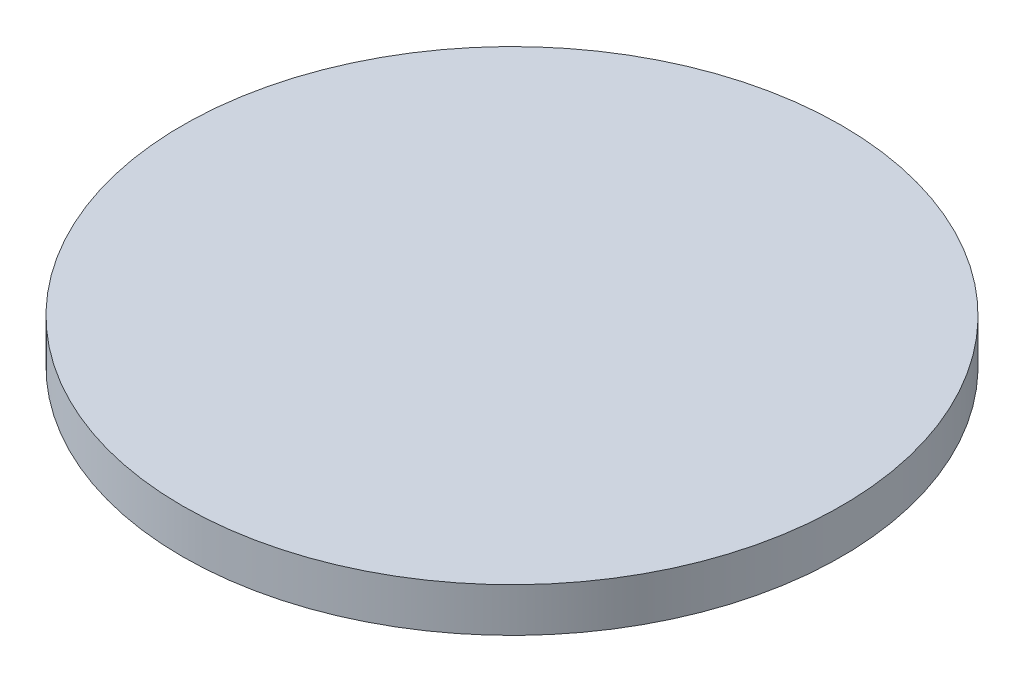
SolidWorks part; units mm, degrees
ref_plane "Front Plane" through (0, 0, 0) normal (0, 0, 1) x (1, 0, 0)
ref_plane "Top Plane" through (0, 0, 0) normal (0, 1, 0) x (1, 0, 0)
ref_plane "Right Plane" through (0, 0, 0) normal (1, 0, 0) x (0, 0, -1)
sketch "Sketch1" plane through (0, 0, 0) normal (0, 1, 0) x (1, 0, 0)
  circle A0 centre (0, 0) radius 15
  dimension "D1" = 30
extrude "Boss-Extrude1" add sketch "Sketch1" along normal blind 2
